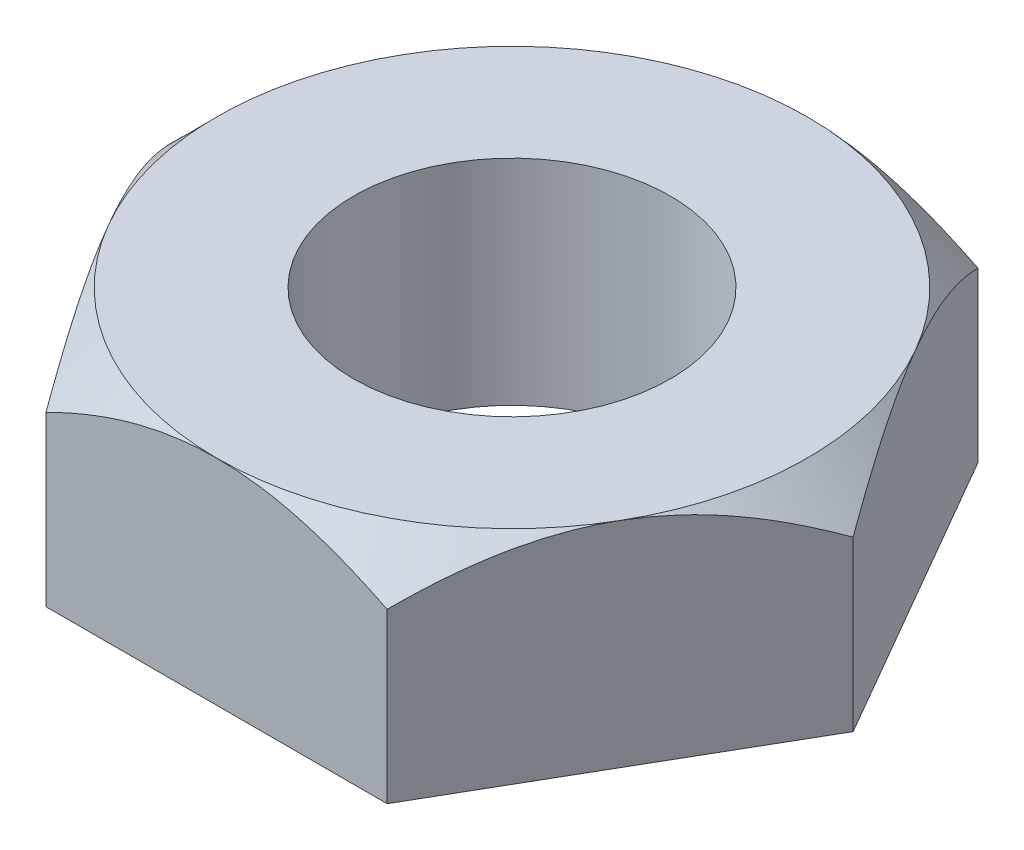
SolidWorks part; units mm, degrees
ref_plane "Front Plane" through (0, 0, 0) normal (0, 0, 1) x (1, 0, 0)
ref_plane "Top Plane" through (0, 0, 0) normal (0, 1, 0) x (1, 0, 0)
ref_plane "Right Plane" through (0, 0, 0) normal (1, 0, 0) x (0, 0, -1)
sketch "Sketch1" plane through (0, 0, 0) normal (0, 1, 0) x (1, 0, 0)
  line L1 (19.9186, 34.5) -> (-19.9186, 34.5)
  line L2 (-19.9186, 34.5) -> (-39.8372, 0)
  line L3 (-39.8372, 0) -> (-19.9186, -34.5)
  line L4 (-19.9186, -34.5) -> (19.9186, -34.5)
  line L5 (19.9186, -34.5) -> (39.8372, 0)
  line L6 (39.8372, 0) -> (19.9186, 34.5)
  circle A0 centre (0, 0) radius 34.5 construction
  dimension "D1" = 69
extrude "Boss-Extrude1" add sketch "Sketch1" along normal blind 25
sketch "Sketch2" plane through (0, 25, 0) normal (0, 1, 0) x (1, 0, 0)
  line L0 (-19.9186, 34.5) -> (-39.8372, 0) construction
  circle A0 centre (0, 0) radius 34.5
extrude "Cut-Extrude1" cut sketch "Sketch2" against normal blind 25 draft 45 flip side to cut
sketch "Sketch3" plane through (0, 25, 0) normal (0, 1, 0) x (1, 0, 0)
  circle A0 centre (0, 0) radius 18.5
  dimension "D1" = 37
extrude "Cut-Extrude2" cut sketch "Sketch3" against normal through all
